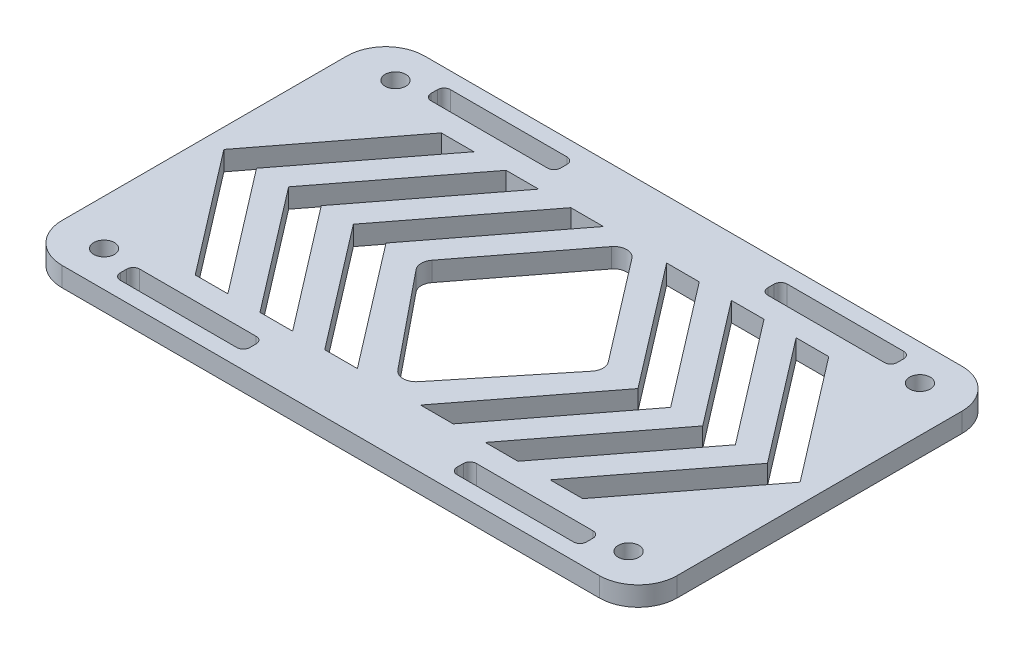
SolidWorks part; units mm, degrees
ref_plane "前视基准面" through (0, 0, 0) normal (0, 0, 1) x (1, 0, 0)
ref_plane "上视基准面" through (0, 0, 0) normal (0, 1, 0) x (1, 0, 0)
ref_plane "右视基准面" through (0, 0, 0) normal (1, 0, 0) x (0, 0, -1)
sketch "草图1" plane through (0, 0, 0) normal (0, 1, 0) x (1, 0, 0)
  line L0 (0, -25.5268) -> (0, -40.3437) construction
  line L1 (-47.5, -28) -> (47.5, -28)
  line L2 (-47.5, -28) -> (-47.5, 28)
  line L3 (-47.5, 28) -> (47.5, 28)
  line L4 (47.5, -28) -> (47.5, 28)
  line L5 (-47.5, -28) -> (47.5, 28) construction
  line L6 (-47.5, 28) -> (47.5, -28) construction
  line L7 (34.1432, 0) -> (46.8663, 0) construction
  circle A0 centre (-40.5, 22.5) radius 1.6
  circle A2 centre (-40.5, -22.5) radius 1.6
  circle A3 centre (40.5, -22.5) radius 1.6
  circle A5 centre (40.5, 22.5) radius 1.6
  point P0 (0, 0)
  dimension "D1" = 3.2
  dimension "D3" = 56
  dimension "D4" = 95
  dimension "D5" = 45
  dimension "D6" = 81
extrude "凸台-拉伸1" add sketch "草图1" along normal blind 3
fillet "圆角1" radius 6 4 edges at (-47.5, 1.5, -28) (47.5, 1.5, -28) (47.5, 1.5, 28) (-47.5, 1.5, 28)
sketch "草图2" plane through (0, 3, 0) normal (0, 1, 0) x (1, 0, 0)
  line L0 (8.6259, 0) -> (23.0772, 0) construction
  line L1 (0, -10.548) -> (0, -28.7904) construction
  line L2 (36, 25.5) -> (16, 25.5)
  line L3 (-36, 22.5) -> (-16, 22.5)
  line L4 (-36, 22.5) -> (-36, 25.5)
  line L5 (-36, 25.5) -> (-16, 25.5)
  line L6 (-16, 22.5) -> (-16, 25.5)
  line L7 (-36, 22.5) -> (-16, 25.5) construction
  line L8 (-36, 25.5) -> (-16, 22.5) construction
  line L9 (16, 22.5) -> (16, 25.5)
  line L10 (36, 22.5) -> (16, 22.5)
  line L11 (36, 22.5) -> (36, 25.5)
  line L12 (-36, -25.5) -> (-16, -25.5)
  line L13 (-16, -22.5) -> (-16, -25.5)
  line L14 (-36, -22.5) -> (-16, -22.5)
  line L15 (-36, -22.5) -> (-36, -25.5)
  line L16 (36, -22.5) -> (36, -25.5)
  line L17 (36, -22.5) -> (16, -22.5)
  line L18 (16, -22.5) -> (16, -25.5)
  line L19 (36, -25.5) -> (16, -25.5)
  line L20 (-39.4581, 0) -> (-24.8789, 19)
  line L21 (41.5, 28) -> (-41.5, 28) construction
  line L22 (-44.5, 0) -> (-29.9208, 19)
  line L23 (-44.5, 0) -> (-29.9208, -19)
  line L24 (-29.9208, 19) -> (-24.8789, 19)
  line L25 (-39.4581, 0) -> (-24.8789, -19)
  line L26 (-29.9208, -19) -> (-24.8789, -19)
  line L27 (-19.9208, -19) -> (-14.8789, -19)
  line L28 (-29.4581, 0) -> (-14.8789, -19)
  line L29 (-29.4581, 0) -> (-14.8789, 19)
  line L30 (-19.9208, 19) -> (-14.8789, 19)
  line L31 (-34.5, 0) -> (-19.9208, 19)
  line L32 (-34.5, 0) -> (-19.9208, -19)
  line L33 (-9.9208, -19) -> (-4.8789, -19)
  line L34 (-19.4581, 0) -> (-4.8789, -19)
  line L35 (-19.4581, 0) -> (-4.8789, 19)
  line L36 (-9.9208, 19) -> (-4.8789, 19)
  line L37 (-24.5, 0) -> (-9.9208, 19)
  line L38 (-24.5, 0) -> (-9.9208, -19)
  line L39 (-29.9208, -19) -> (-19.9208, -19) construction
  line L40 (44.5, 0) -> (29.9208, -19)
  line L41 (44.5, 0) -> (29.9208, 19)
  line L42 (29.9208, 19) -> (24.8789, 19)
  line L43 (39.4581, 0) -> (24.8789, 19)
  line L44 (39.4581, 0) -> (24.8789, -19)
  line L45 (29.9208, -19) -> (24.8789, -19)
  line L46 (34.5, 0) -> (19.9208, -19)
  line L47 (34.5, 0) -> (19.9208, 19)
  line L48 (19.9208, 19) -> (14.8789, 19)
  line L49 (29.4581, 0) -> (14.8789, 19)
  line L50 (29.4581, 0) -> (14.8789, -19)
  line L51 (19.9208, -19) -> (14.8789, -19)
  line L52 (24.5, 0) -> (9.9208, -19)
  line L53 (24.5, 0) -> (9.9208, 19)
  line L54 (9.9208, 19) -> (4.8789, 19)
  line L55 (19.4581, 0) -> (4.8789, 19)
  line L56 (19.4581, 0) -> (4.8789, -19)
  line L57 (9.9208, -19) -> (4.8789, -19)
  line L58 (-47.5, 22) -> (-47.5, -22) construction
  line L59 (-14.5792, 0) -> (0, 19)
  line L60 (0, 19) -> (14.5792, 0)
  line L61 (14.5792, 0) -> (0, -18)
  line L62 (0, -18) -> (-14.5792, 0)
  point P4 (-26, 24)
  dimension "D5" = 2.5
  dimension "D1" = 20
  dimension "D2" = 3
  dimension "D3" = 45
  dimension "D4" = 32
  dimension "D6" = 105
  dimension "D7" = 19
  dimension "D9" = 10
  dimension "D10" = 4
  dimension "D11" = 3
  dimension "D8" = 3
extrude "切除-拉伸1" cut sketch "草图2" against normal through all
fillet "圆角2" radius 2 4 edges at (0, 1.5, 18) (-14.5792, 1.5, 0) (14.5792, 1.5, 0) (0, 1.5, -19)
fillet "圆角3" radius 1 16 edges at (16, 1.5, -25.5) (-36, 1.5, 22.5) (16, 1.5, 22.5) (36, 1.5, -22.5) (36, 1.5, 25.5) (-16, 1.5, 25.5) (-16, 1.5, -22.5) (16, 1.5, 25.5) (16, 1.5, -22.5) (-36, 1.5, -22.5) (-36, 1.5, 25.5) (-16, 1.5, 22.5) (36, 1.5, 22.5) (36, 1.5, -25.5) (-16, 1.5, -25.5) (-36, 1.5, -25.5)
